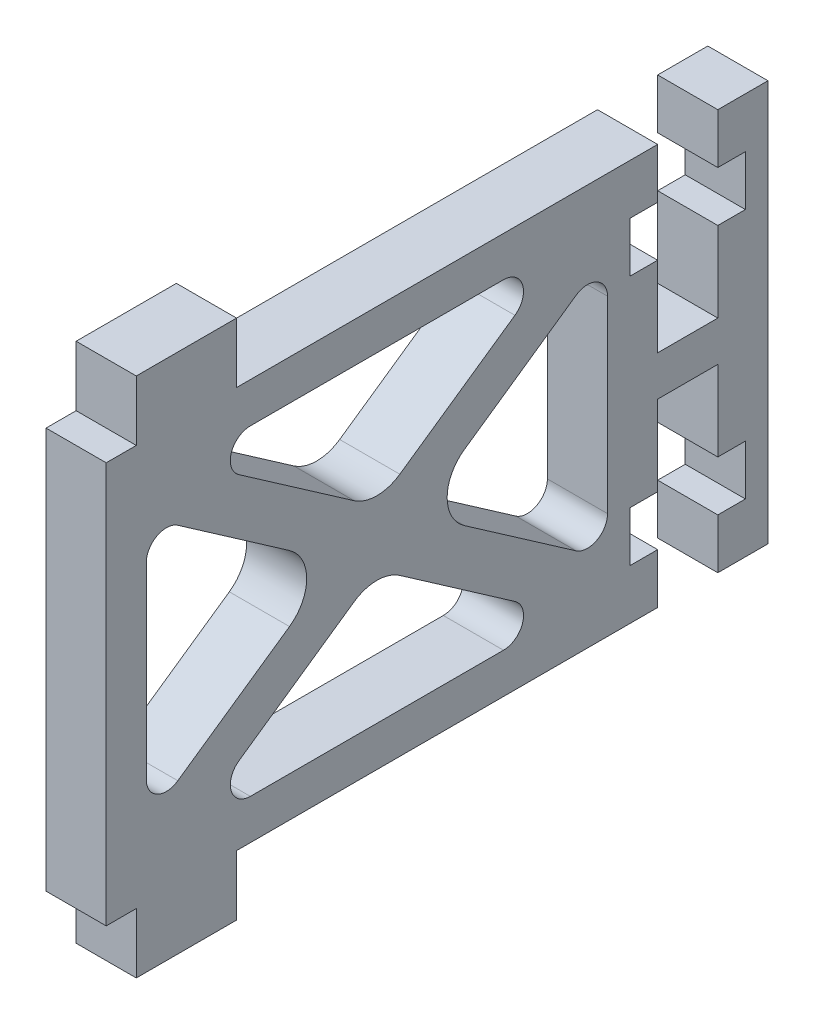
SolidWorks part; units mm, degrees
ref_plane "Plano frontal" through (0, 0, 0) normal (0, 0, 1) x (1, 0, 0)
ref_plane "Plano superior" through (0, 0, 0) normal (0, 1, 0) x (1, 0, 0)
ref_plane "Plano direito" through (0, 0, 0) normal (1, 0, 0) x (0, 0, -1)
sketch "Esboço1" plane through (0, 0, 0) normal (1, 0, 0) x (0, 0, -1)
  line L0 (-15.5931, 2.1259) -> (-17.0931, 2.1259)
  line L1 (-10.5931, 5.1259) -> (-15.5931, 5.1259)
  line L2 (15.9069, -17.8741) -> (15.9069, 2.1259)
  line L3 (-17.0931, -17.8741) -> (-17.0931, 2.1259)
  line L4 (14.7819, -2.8741) -> (14.7819, -0.3741)
  line L5 (10.4069, 2.1259) -> (10.4069, -0.3741)
  line L6 (10.4069, -8.8741) -> (10.4069, -10.3741)
  line L7 (13.4069, -10.3741) -> (13.4069, -8.8741)
  line L8 (9.0319, -2.8741) -> (10.4069, -2.8741)
  line L9 (14.7819, -0.3741) -> (13.4069, -0.3741)
  line L10 (9.0319, -0.3741) -> (9.0319, -2.8741)
  line L11 (10.4069, -0.3741) -> (9.0319, -0.3741)
  line L12 (10.4069, -5.3741) -> (10.4069, -6.8741)
  line L13 (13.4069, -2.8741) -> (14.7819, -2.8741)
  line L14 (10.4069, -0.3741) -> (9.0319, -0.3741)
  line L15 (10.4069, -6.8741) -> (10.4069, -5.3741)
  line L16 (-9.0931, -17.8741) -> (-10.5931, -17.8741)
  line L17 (10.4069, 2.1259) -> (-9.0931, 2.1259)
  line L19 (7.4069, 36.3259) -> (9.9069, 36.3259)
  line L20 (13.4069, -6.8741) -> (13.4069, -5.3741)
  line L22 (13.4069, -17.8741) -> (15.9069, -17.8741)
  line L23 (13.4069, -15.3741) -> (13.4069, -17.8741)
  line L33 (10.4069, 2.1259) -> (7.9069, 2.1259)
  line L47 (13.4069, -0.3741) -> (13.4069, 2.1259)
  line L48 (13.4069, 2.1259) -> (15.9069, 2.1259)
  line L49 (10.4069, -17.8741) -> (7.9069, -17.8741)
  line L51 (7.4069, -17.8741) -> (9.9069, -17.8741)
  line L53 (10.4069, -17.8741) -> (-9.0931, -17.8741)
  line L55 (10.4069, -15.3741) -> (9.0319, -15.3741)
  line L57 (13.4069, -12.8741) -> (14.7819, -12.8741)
  line L58 (10.4069, -10.3741) -> (10.4069, -8.8741)
  line L59 (10.4069, -15.3741) -> (9.0319, -15.3741)
  line L60 (9.0319, -15.3741) -> (9.0319, -12.8741)
  line L61 (14.7819, -15.3741) -> (13.4069, -15.3741)
  line L62 (9.0319, -12.8741) -> (10.4069, -12.8741)
  line L63 (13.4069, -5.3741) -> (13.4069, -6.8741)
  line L64 (13.4069, -8.8741) -> (13.4069, -10.3741)
  line L65 (10.4069, -17.8741) -> (10.4069, -15.3741)
  line L66 (14.7819, -12.8741) -> (14.7819, -15.3741)
  line L67 (-15.5931, -17.8741) -> (-17.0931, -17.8741)
  line L68 (-10.5931, -20.8741) -> (-15.5931, -20.8741)
  line L69 (13.4069, -8.8741) -> (10.4069, -8.8741)
  line L92 (-9.0931, 2.1259) -> (-10.5931, 2.1259)
  line L93 (-10.5931, -20.8741) -> (-10.5931, -17.8741)
  line L94 (-15.5931, 5.1259) -> (-10.5931, 5.1259)
  line L95 (-15.5931, 2.1259) -> (-15.5931, 5.1259)
  line L97 (-10.5931, 5.1259) -> (-10.5931, 2.1259)
  line L98 (-15.5931, -17.8741) -> (-15.5931, -20.8741)
  line L99 (-15.5931, -20.8741) -> (-10.5931, -20.8741)
  line L100 (-10.5931, -20.8741) -> (-15.5931, -20.8741)
  line L101 (13.4069, -6.8741) -> (10.4069, -6.8741)
  line L102 (13.4069, -10.3741) -> (13.4069, -12.8741)
  line L103 (10.4069, -10.3741) -> (10.4069, -12.8741)
  line L104 (13.4069, -5.3741) -> (13.4069, -2.8741)
  line L105 (10.4069, -5.3741) -> (10.4069, -3.2561)
  line L106 (10.4069, -3.2561) -> (10.4069, -2.8741)
  line L107 (-7.9532, -9.5159) -> (-13.5221, -13.3899)
  line L108 (-4.7353, -10.0599) -> (-10.4756, -14.0532)
  line L109 (0.767, -9.5159) -> (6.3358, -13.3899)
  line L110 (7.9069, -10.3741) -> (7.9069, -3.1792)
  line L112 (7.9069, -10.3741) -> (7.9069, -12.569)
  line L113 (3.2893, -1.695) -> (-2.451, -5.6883)
  line L114 (2.7182, -15.8741) -> (-9.9045, -15.8741)
  line L115 (-15.0931, -12.569) -> (-15.0931, -3.1792)
  line L116 (-9.9045, 0.1259) -> (2.7182, 0.1259)
  line L117 (-10.4756, -1.695) -> (-4.7353, -5.6883)
  line L118 (-13.5221, -2.3583) -> (-7.9532, -6.2323)
  line L119 (6.3358, -2.3583) -> (0.767, -6.2323)
  line L121 (-2.451, -10.0599) -> (3.2893, -14.0532)
  arc A42 (-4.7353, -5.6883) -> (-2.451, -5.6883) centre (-3.5931, -4.0465) ccw
  arc A43 (-7.9532, -6.2323) -> (-7.9532, -9.5159) centre (-9.0954, -7.8741) cw
  arc A44 (0.767, -9.5159) -> (0.767, -6.2323) centre (1.9091, -7.8741) cw
  arc A45 (-2.451, -10.0599) -> (-4.7353, -10.0599) centre (-3.5931, -11.7017) ccw
  arc A46 (2.7182, -15.8741) -> (3.2893, -14.0532) centre (2.7182, -14.8741) ccw
  arc A47 (-10.4756, -14.0532) -> (-9.9045, -15.8741) centre (-9.9045, -14.8741) ccw
  arc A48 (7.9069, -12.569) -> (6.3358, -13.3899) centre (6.9069, -12.569) cw
  arc A49 (-15.0931, -12.569) -> (-13.5221, -13.3899) centre (-14.0931, -12.569) ccw
  arc A50 (-13.5221, -2.3583) -> (-15.0931, -3.1792) centre (-14.0931, -3.1792) ccw
  arc A51 (-10.4756, -1.695) -> (-9.9045, 0.1259) centre (-9.9045, -0.8741) cw
  arc A52 (3.2893, -1.695) -> (2.7182, 0.1259) centre (2.7182, -0.8741) ccw
  arc A53 (6.3358, -2.3583) -> (7.9069, -3.1792) centre (6.9069, -3.1792) cw
  point P16 (9.9069, 0.6759)
  point P27 (-5.5931, -7.8741)
  point P39 (-3.5931, -9.2654)
  point P52 (5.645, 0.1259)
  point P101 (15.9069, 0.6759)
  dimension "D1" = 2
  dimension "D2" = 2
  dimension "D3" = 2
  dimension "D4" = 2
  dimension "D5" = 1
  dimension "D6" = 1
  dimension "D7" = 1
  dimension "D8" = 1
  dimension "D9" = 1
  dimension "D10" = 1
  dimension "D11" = 1
  dimension "D12" = 1
extrude "Ressalto-extrusão1" add sketch "Esboço1" along normal blind 3
